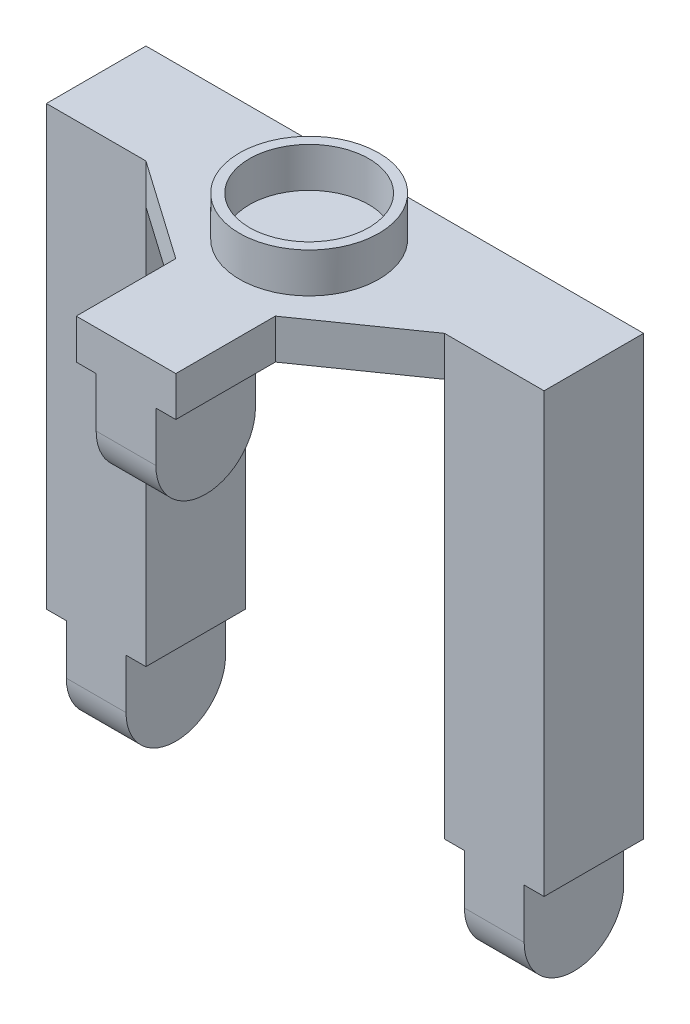
SolidWorks part; units mm, degrees
ref_plane "Front" through (0, 0, 0) normal (0, 0, 1) x (1, 0, 0)
ref_plane "Top" through (0, 0, 0) normal (0, 1, 0) x (1, 0, 0)
ref_plane "Right" through (0, 0, 0) normal (1, 0, 0) x (0, 0, -1)
sketch "草图1" plane through (0, 0, 0) normal (0, 1, 0) x (1, 0, 0)
  line L0 (-31.9558, 0) -> (0, 0) construction
  line L1 (-25, 5) -> (-15, 5)
  line L2 (-25, 5) -> (-25, -5)
  line L3 (-25, -5) -> (-15, -5)
  line L4 (-15, 5) -> (-15, -5)
  line L5 (15, 5) -> (25, 5)
  line L6 (15, 5) -> (15, -5)
  line L7 (15, -5) -> (25, -5)
  line L8 (25, 5) -> (25, -5)
  line L9 (-5, -12) -> (5, -12) construction
  line L10 (-5, -12) -> (-5, -22) construction
  line L11 (-5, -22) -> (5, -22) construction
  line L12 (5, -12) -> (5, -22) construction
  line L13 (0, 0) -> (0, 15.9462) construction
  dimension "D1" = 10
  dimension "D2" = 10
  dimension "D3" = 10
  dimension "D4" = 10
  dimension "D5" = 5
  dimension "D6" = 5
  dimension "D7" = 10
  dimension "D8" = 10
  dimension "D9" = 5
  dimension "D10" = 15
  dimension "D11" = 15
  dimension "D12" = 12
sketch "草图2" plane through (0, 0, 0) normal (0, 1, 0) x (1, 0, 0)
  line L0 (-25, -5) -> (-25, 23.5912) construction
  line L1 (25, -5) -> (25, 17.5149) construction
  line L2 (-25, 5) -> (25, 5) construction
  line L12 (-5, -22) -> (5, -22)
  line L19 (25, -5) -> (25, 5)
  line L20 (25, 5) -> (-25, 5)
  line L21 (-25, 5) -> (-25, -5)
  line L22 (-25, -5) -> (-15, -5)
  line L23 (-15, -5) -> (-5, -12)
  line L24 (-5, -12) -> (-5, -22)
  line L25 (5, -22) -> (5, -12)
  line L26 (5, -12) -> (15, -5)
  line L27 (15, -5) -> (25, -5)
extrude "凸台-拉伸1" add sketch "草图2" along normal blind 4
extrude "凸台-拉伸2" add sketch "草图1" against normal blind 50
sketch "草图6" plane through (0, 0, 0) normal (0, -1, 0) x (1, 0, 0)
  line L1 (-5, 22) -> (5, 22)
  line L2 (-5, 22) -> (-5, 12)
  line L3 (-5, 12) -> (5, 12)
  line L4 (5, 22) -> (5, 12)
extrude "凸台-拉伸4" add sketch "草图6" along normal blind 10
sketch "草图7" plane through (0, 0, -5) normal (0, 0, -1) x (-1, 0, 0)
  line L0 (-20, -50) -> (-20, 5.1391) construction
  line L1 (-25, -50) -> (-15, -50) construction
  line L2 (0, -10) -> (0, 5.1391) construction
  line L3 (5, -10) -> (-5, -10) construction
  line L4 (20, -50) -> (20, 4) construction
  line L5 (15, -50) -> (25, -50) construction
  line L6 (-25, 4) -> (25, 4) construction
  line L7 (25, 4) -> (25, -50) construction
  line L8 (-25, -50) -> (-23, -50)
  line L9 (-25, -50) -> (-25, -40)
  line L10 (-25, -40) -> (-23, -40)
  line L11 (25, -50) -> (25, -40)
  line L12 (-15, 0) -> (15, 0) construction
  line L13 (-7.9288, 0) -> (-3, 0)
  line L14 (-7.9288, 0) -> (-7.9288, -10)
  line L15 (-7.9288, -10) -> (-3, -10)
  line L16 (8.693, 0) -> (8.693, -10)
  line L17 (3, -10) -> (8.693, -10)
  line L19 (-23, -50) -> (-23, -40)
  line L21 (-17, -50) -> (-17, -40)
  line L23 (17, -50) -> (17, -40)
  line L25 (23, -50) -> (23, -40)
  line L27 (-3, -10) -> (-3, 0)
  line L29 (3, -10) -> (3, 0)
  line L30 (3, 0) -> (8.693, 0)
  line L31 (23, -50) -> (25, -50)
  line L32 (23, -40) -> (25, -40)
  line L33 (-17, -50) -> (17, -50)
  line L34 (-17, -40) -> (17, -40)
  line L35 (0, 0) -> (0, -63.8549) construction
  dimension "D1" = 10
  dimension "D2" = 6
  dimension "D3" = 3
  dimension "D4" = 6
  dimension "D5" = 3
  dimension "D6" = 6
  dimension "D7" = 3
extrude "切除-拉伸3" cut sketch "草图7" against normal through all
sketch "草图8" plane through (25, 0, 0) normal (1, 0, 0) x (0, 0, -1)
  line L2 (-22, -5) -> (-22, -14.4096)
  line L3 (-22, -14.4096) -> (-12, -14.4096)
  line L4 (-12, -5) -> (-12, -14.4096)
  line L6 (-5, -45) -> (-5, -53.4809)
  line L7 (-5, -53.4809) -> (5, -53.4809)
  line L8 (5, -45) -> (5, -53.4809)
  arc A0 (-22, -5) -> (-12, -5) centre (-17, -5) ccw
  arc A1 (-5, -45) -> (5, -45) centre (0, -45) ccw
extrude "切除-拉伸4" cut sketch "草图8" against normal through all
sketch "草图9" plane through (0, 4, 0) normal (0, 1, 0) x (1, 0, 0)
  circle A0 centre (0, -3.6) radius 6
  circle A1 centre (0, -3.6) radius 7
extrude "凸台-拉伸5" add sketch "草图9" along normal blind 4
